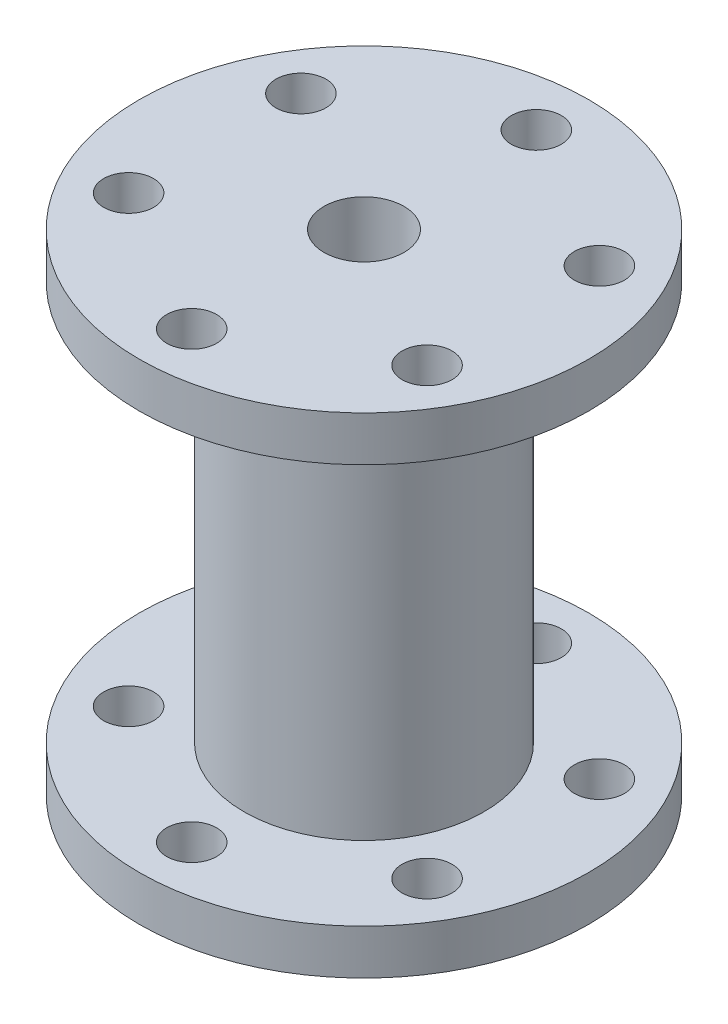
SolidWorks part; units mm, degrees
ref_plane "Front Plane" through (0, 0, 0) normal (0, 0, 1) x (1, 0, 0)
ref_plane "Top Plane" through (0, 0, 0) normal (0, 1, 0) x (1, 0, 0)
ref_plane "Right Plane" through (0, 0, 0) normal (1, 0, 0) x (0, 0, -1)
sketch "Sketch1" plane through (0, 0, 0) normal (0, 1, 0) x (1, 0, 0)
  circle A0 centre (0, 0) radius 22.5
  dimension "D1" = 45
extrude "Boss-Extrude1" add sketch "Sketch1" along normal blind 4.5
sketch "Sketch2" plane through (0, 4.5, 0) normal (0, 1, 0) x (1, 0, 0)
  circle A0 centre (0, 0) radius 12
extrude "Boss-Extrude2" add sketch "Sketch2" along normal blind 40
sketch "Sketch3" plane through (0, 44.5, 0) normal (0, 1, 0) x (1, 0, 0)
  circle A0 centre (0, 0) radius 22.5
extrude "Boss-Extrude3" add sketch "Sketch3" along normal blind 4.5
sketch "Sketch4" plane through (0, 0, 0) normal (0, -1, 0) x (1, 0, 0)
  circle A0 centre (0, 0) radius 4
  dimension "D1" = 8
extrude "Cut-Extrude1" cut sketch "Sketch4" against normal blind 60.5
sketch "Sketch5" plane through (0, 0, 0) normal (0, -1, 0) x (1, 0, 0)
  line L0 (0, 0) -> (0, 17.25) construction
  circle A0 centre (0, 17.25) radius 2.5
  circle A1 centre (14.9389, 8.625) radius 2.5
  circle A2 centre (14.9389, -8.625) radius 2.5
  circle A3 centre (0, -17.25) radius 2.5
  circle A4 centre (-14.9389, -8.625) radius 2.5
  circle A5 centre (-14.9389, 8.625) radius 2.5
  point P17 (0, 0)
  dimension "D2" = 5
  dimension "D1" = 17.25
  dimension "D3" = 6
extrude "Cut-Extrude2" cut sketch "Sketch5" against normal blind 60.5
